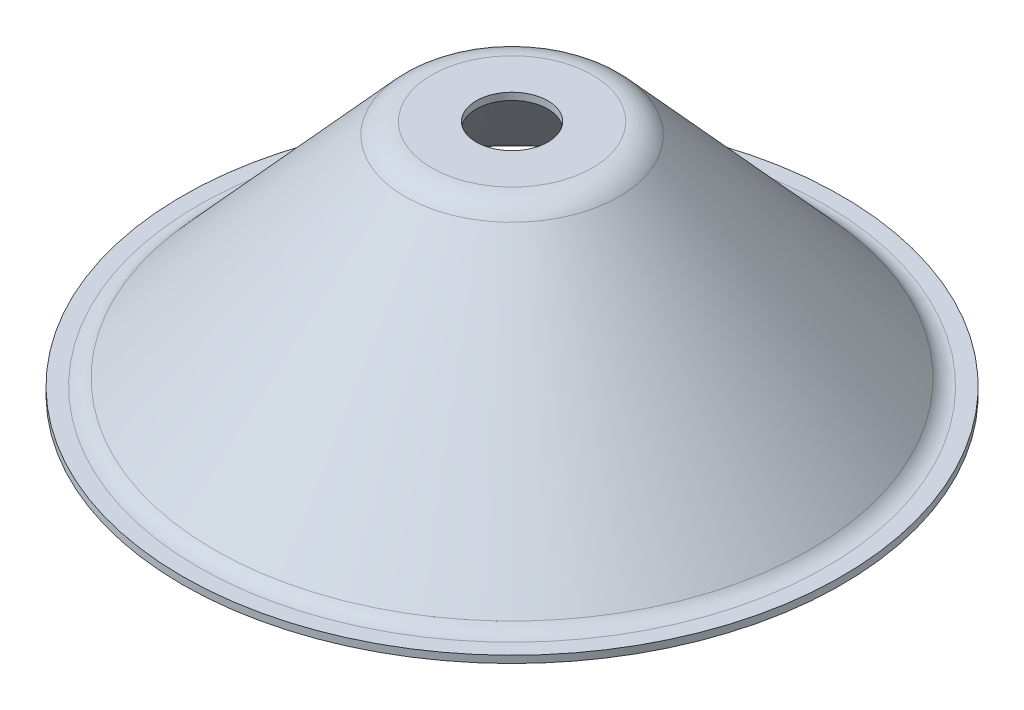
SolidWorks part; units mm, degrees
material "A286 Iron Base Superalloy"
ref_plane "Front Plane" through (0, 0, 0) normal (0, 0, 1) x (1, 0, 0)
ref_plane "Top Plane" through (0, 0, 0) normal (0, 1, 0) x (1, 0, 0)
ref_plane "Right Plane" through (0, 0, 0) normal (1, 0, 0) x (0, 0, -1)
sketch "Sketch1" plane through (0, 0, 0) normal (0, 0, 1) x (1, 0, 0)
  line L0 (0, 23.4158) -> (0, -25.7921) construction
  line L2 (14.1907, -1.3139) -> (40.8093, -30.6861)
  line L5 (43.7732, -32) -> (46, -32)
  line L6 (11.2268, 0) -> (5, 0)
  arc A0 (40.8093, -30.6861) -> (43.7732, -32) centre (43.7732, -28) ccw
  arc A1 (11.2268, 0) -> (14.1907, -1.3139) centre (11.2268, -4) cw
  point P13 (42, -32)
  point P16 (13, 0)
  dimension "D6" = 4
  dimension "D1" = 5
  dimension "D2" = 42
  dimension "D3" = 13
  dimension "D4" = 32
  dimension "D5" = 46
revolve "Revolve-Thin1" add sketch "Sketch1" angle 360 about L0 wall 1
